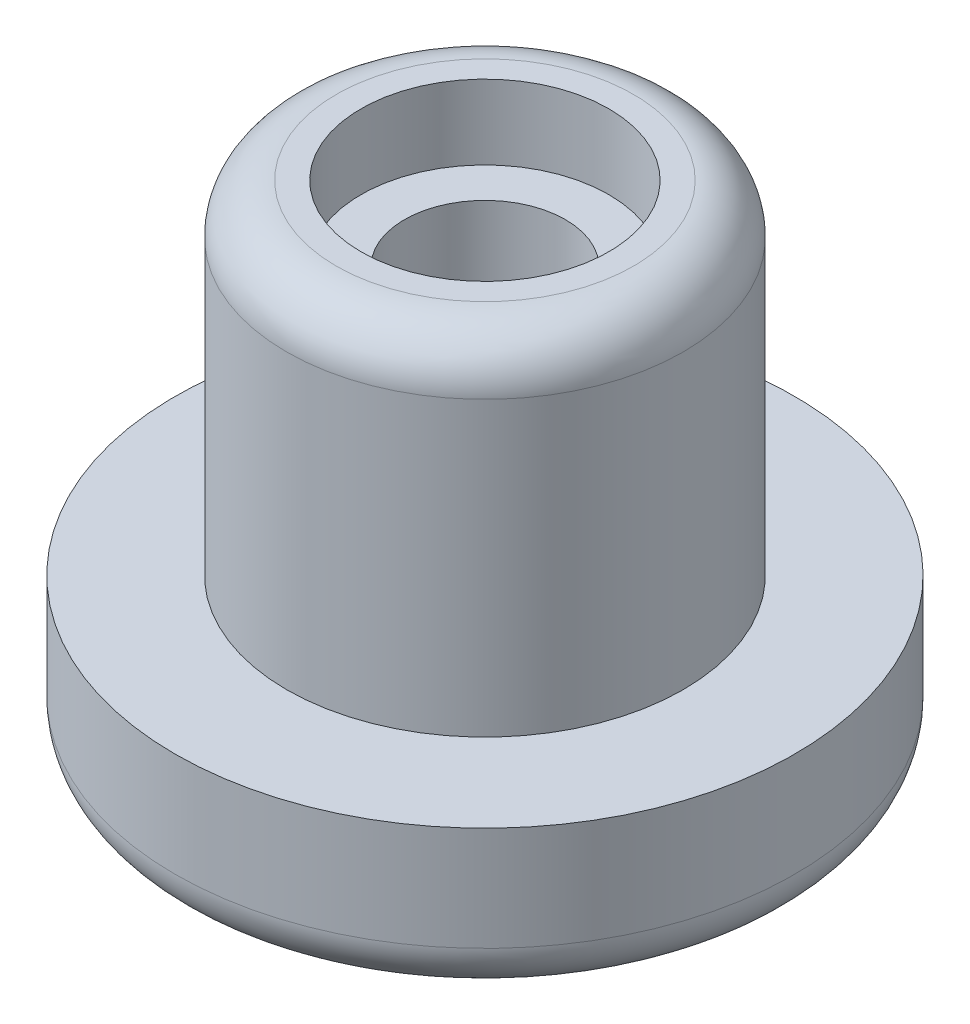
SolidWorks part; units mm, degrees
ref_plane "Front Plane" through (0, 0, 0) normal (0, 0, 1) x (1, 0, 0)
ref_plane "Top Plane" through (0, 0, 0) normal (0, 1, 0) x (1, 0, 0)
ref_plane "Right Plane" through (0, 0, 0) normal (1, 0, 0) x (0, 0, -1)
sketch "Sketch1" plane through (0, 0, 0) normal (0, 1, 0) x (1, 0, 0)
  circle A0 centre (0, 0) radius 12.7
  circle A1 centre (0, 0) radius 31.75
  dimension "D1" = 63.5
  dimension "D2" = 25.4
extrude "Boss-Extrude1" add sketch "Sketch1" along normal blind 15.748
sketch "Sketch2" plane through (0, 15.748, 0) normal (0, 1, 0) x (1, 0, 0)
  circle A0 centre (0, 0) radius 12.7
  circle A1 centre (0, 0) radius 20.32
  dimension "D1" = 40.64
extrude "Boss-Extrude2" add sketch "Sketch2" along normal blind 35.052
sketch "Sketch3" plane through (0, 0, 0) normal (0, -1, 0) x (1, 0, 0)
  circle A0 centre (0, 0) radius 12.7
  circle A1 centre (0, 0) radius 8.255
  dimension "D1" = 16.51
extrude "Boss-Extrude3" add sketch "Sketch3" against normal blind 43.18 separate body
fillet "Fillet1" radius 5.08 1 edges at (0, 0, 31.75)
fillet "Fillet2" radius 5.08 1 edges at (0, 50.8, 20.32)
